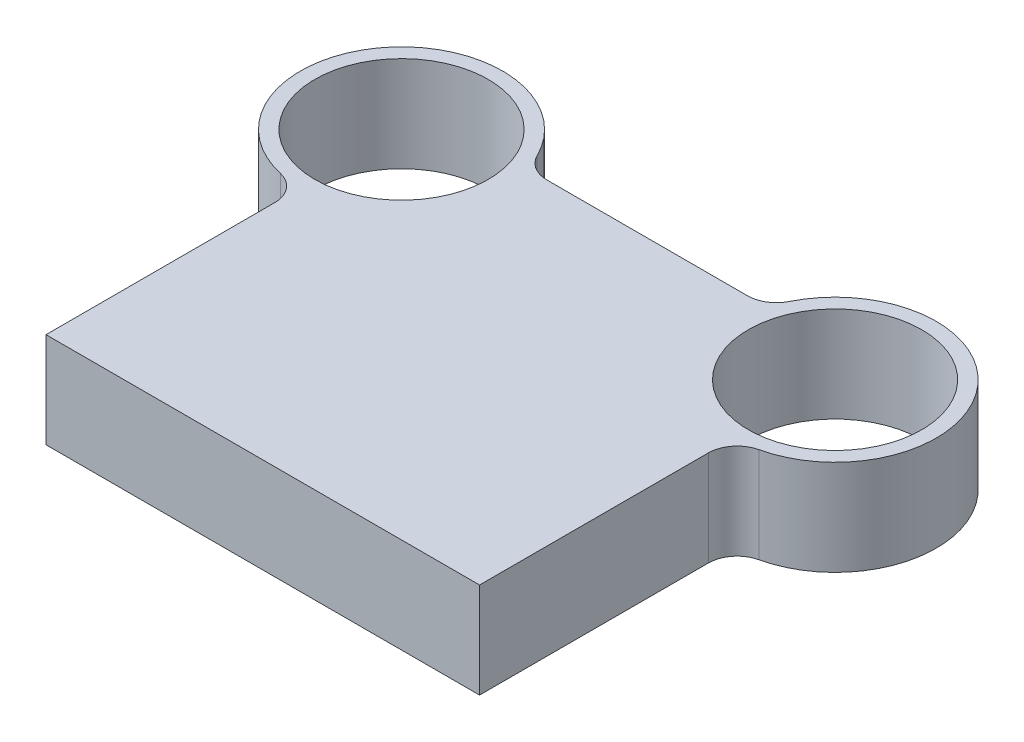
SolidWorks part; units mm, degrees
ref_plane "Front Plane" through (0, 0, 0) normal (0, 0, 1) x (1, 0, 0)
ref_plane "Top Plane" through (0, 0, 0) normal (0, 1, 0) x (1, 0, 0)
ref_plane "Right Plane" through (0, 0, 0) normal (1, 0, 0) x (0, 0, -1)
sketch "Sketch1" plane through (0, 0, 0) normal (0, 1, 0) x (1, 0, 0)
  line L0 (75, 0) -> (-75, 0)
  line L1 (-75, 0) -> (-75, 88)
  line L2 (0, 0) -> (0, 133) construction
  line L3 (41.459, 133) -> (-41.459, 133)
  line L4 (75, 0) -> (75, 88)
  arc A0 (-41.459, 133) -> (-75, 88) centre (-75, 123) ccw
  circle A1 centre (-75, 123) radius 30
  arc A2 (41.459, 133) -> (75, 88) centre (75, 123) cw
  circle A3 centre (75, 123) radius 30
  point P12 (0, 133)
  dimension "D1" = 70
  dimension "D2" = 60
  dimension "D3" = 150
  dimension "D4" = 123
  dimension "D5" = 133
  dimension "D6" = 150
extrude "Boss-Extrude1" add sketch "Sketch1" along normal blind 33
fillet "Fillet1" radius 10 4 edges at (75, 16.5, -88) (41.459, 16.5, -133) (-41.459, 16.5, -133) (-75, 16.5, -88)
